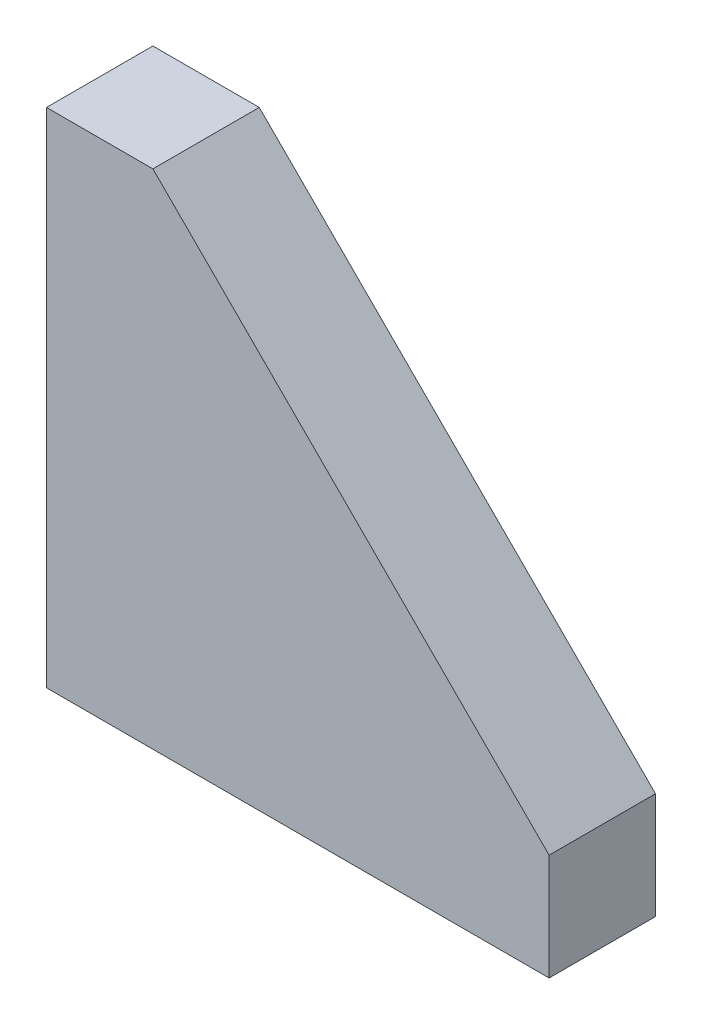
SolidWorks part; units mm, degrees
material "Balsa"
ref_plane "Front Plane" through (0, 0, 0) normal (0, 0, 1) x (1, 0, 0)
ref_plane "Top Plane" through (0, 0, 0) normal (0, 1, 0) x (1, 0, 0)
ref_plane "Right Plane" through (0, 0, 0) normal (1, 0, 0) x (0, 0, -1)
sketch "Sketch1" plane through (0, 0, 0) normal (0, 0, 1) x (1, 0, 0)
  line L0 (0, 0) -> (0, 30)
  line L2 (30, 0) -> (0, 0)
  line L3 (0, 30) -> (6.35, 30)
  line L4 (6.35, 30) -> (30, 6.35)
  line L5 (30, 6.35) -> (30, 0)
  dimension "D1" = 30
  dimension "D2" = 6.35
  dimension "D3" = 6.35
extrude "Boss-Extrude1" add sketch "Sketch1" along normal blind 6.35
